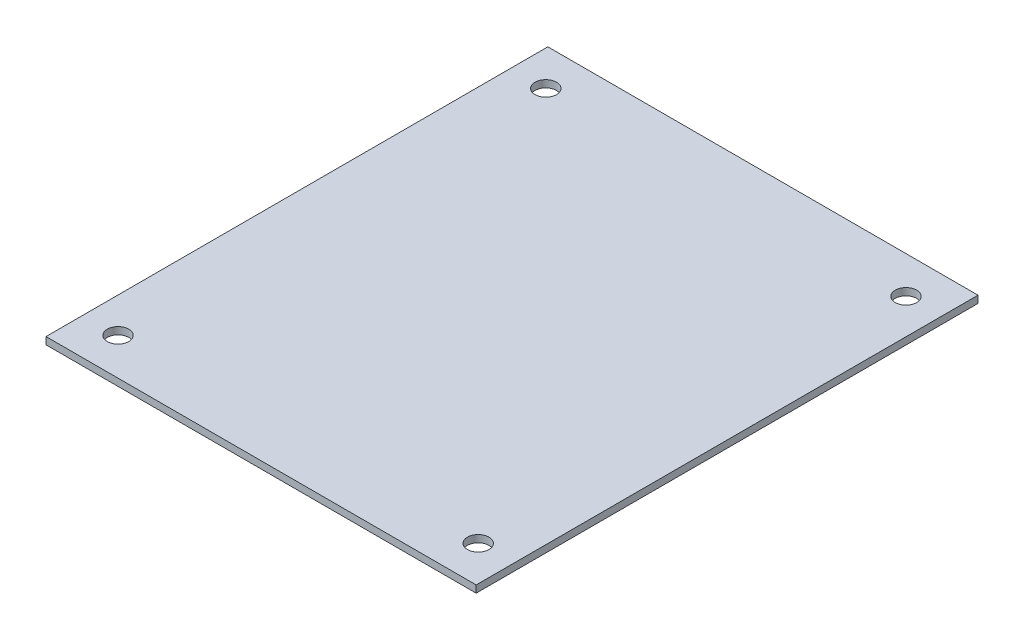
SolidWorks part; units mm, degrees
material "Custom Plastic"
ref_plane "Front Plane" through (0, 0, 0) normal (0, 0, 1) x (1, 0, 0)
ref_plane "Top Plane" through (0, 0, 0) normal (0, 1, 0) x (1, 0, 0)
ref_plane "Right Plane" through (0, 0, 0) normal (1, 0, 0) x (0, 0, -1)
sketch "Sketch1" plane through (0, 0, 0) normal (0, 1, 0) x (1, 0, 0)
  line L1 (-30, 35) -> (30, 35)
  line L2 (-30, 35) -> (-30, -35)
  line L3 (-30, -35) -> (30, -35)
  line L4 (30, 35) -> (30, -35)
  line L5 (-30, 35) -> (30, -35) construction
  line L6 (-30, -35) -> (30, 35) construction
  point P0 (0, 0)
  dimension "D1" = 70
  dimension "D2" = 60
extrude "Boss-Extrude1" add sketch "Sketch1" along normal blind 1
sketch "Sketch2" plane through (0, 1, 0) normal (0, 1, 0) x (1, 0, 0)
  line L0 (-0.55, 0) -> (0.55, 0) construction
  line L1 (0, -0.55) -> (0, 0.55) construction
  circle A0 centre (-25.1193, 29.8326) radius 1.5
  circle A1 centre (-25.1193, -29.8326) radius 1.5
  circle A2 centre (25.1193, 29.8326) radius 1.5
  circle A3 centre (25.1193, -29.8326) radius 1.5
  dimension "D1" = 3
extrude "Cut-Extrude1" cut sketch "Sketch2" against normal blind 1
